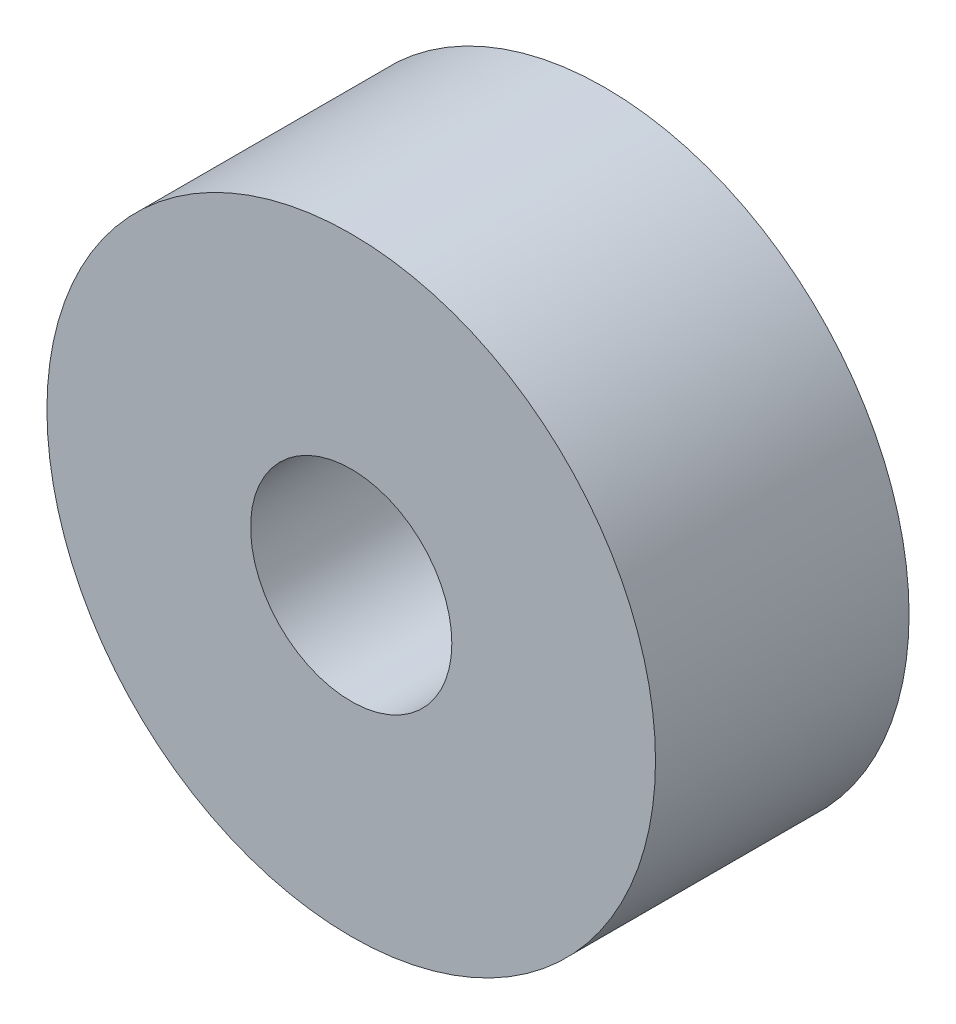
SolidWorks part; units mm, degrees
ref_plane "Front Plane" through (0, 0, 0) normal (0, 0, 1) x (1, 0, 0)
ref_plane "Top Plane" through (0, 0, 0) normal (0, 1, 0) x (1, 0, 0)
ref_plane "Right Plane" through (0, 0, 0) normal (1, 0, 0) x (0, 0, -1)
sketch "Sketch1" plane through (0, 0, 0) normal (0, 0, 1) x (1, 0, 0)
  circle A0 centre (0, 0) radius 4.8
  circle A1 centre (0, 0) radius 1.5875
extrude "Boss-Extrude1" add sketch "Sketch1" along normal blind 4
